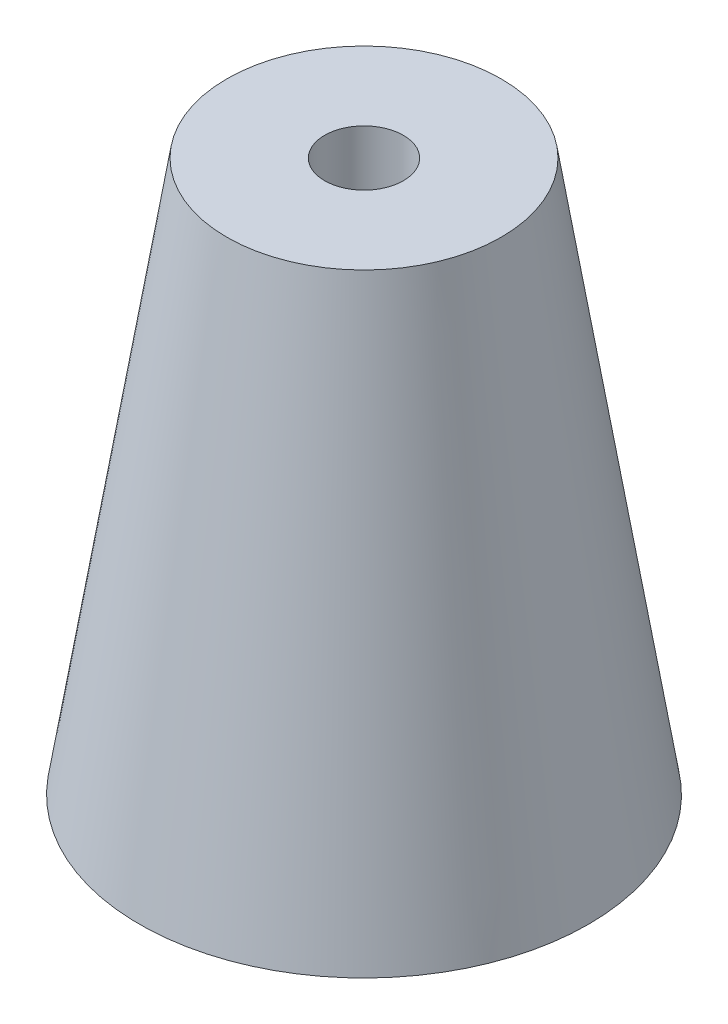
SolidWorks part; units mm, degrees
ref_plane "Front Plane" through (0, 0, 0) normal (0, 0, 1) x (1, 0, 0)
ref_plane "Top Plane" through (0, 0, 0) normal (0, 1, 0) x (1, 0, 0)
ref_plane "Right Plane" through (0, 0, 0) normal (1, 0, 0) x (0, 0, -1)
sketch "Sketch2" plane through (0, 0, 0) normal (0, 0, 1) x (1, 0, 0)
  line L0 (0, 0) -> (36.195, 0)
  line L1 (36.195, 0) -> (22.1192, 88.9)
  line L2 (0, 88.9) -> (0, 0)
  line L3 (0, 88.9) -> (22.1192, 88.9)
  line L4 (22.1192, 88.9) -> (0, 228.6) construction
  line L5 (0, 228.6) -> (0, 88.9) construction
  dimension "D1" = 36.195
  dimension "D2" = 228.6
  dimension "D3" = 88.9
revolve "Revolve1" add sketch "Sketch2" angle 360 about L2
sketch "Sketch3" plane through (0, 0, 0) normal (0, -1, 0) x (1, 0, 0)
  circle A0 centre (0, 0) radius 6.35
  dimension "D1" = 12.7
extrude "Cut-Extrude1" cut sketch "Sketch3" against normal through all
shell "Shell1" thickness 1.27
fillet "Fillet1" radius 2.54 2 edges at (21.0344, 87.63, 0) (7.62, 87.63, 0)
